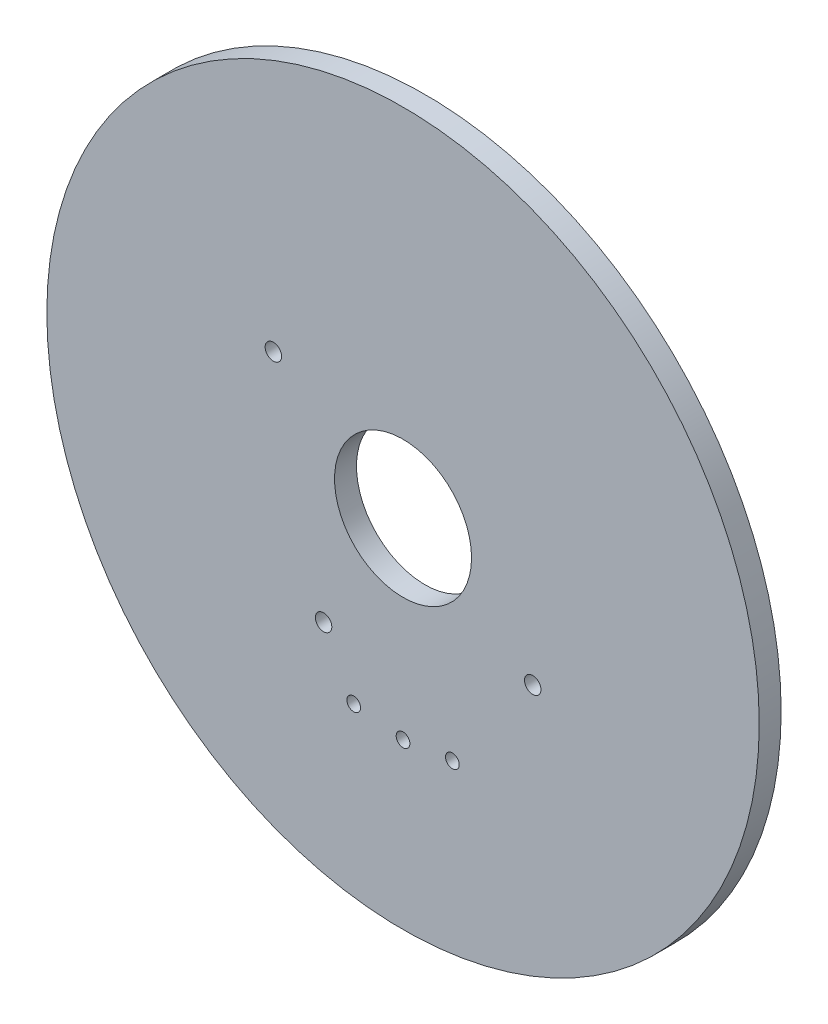
SolidWorks part; units mm, degrees
material "Fibra de vidrio-S"
ref_plane "Alzado" through (0, 0, 0) normal (0, 0, 1) x (1, 0, 0)
ref_plane "Planta" through (0, 0, 0) normal (0, 1, 0) x (1, 0, 0)
ref_plane "Vista lateral" through (0, 0, 0) normal (1, 0, 0) x (0, 0, -1)
sketch "Croquis1" plane through (0, 0, 0) normal (0, 0, 1) x (1, 0, 0)
  circle A0 centre (0, 0) radius 13
  circle A1 centre (0, 0) radius 2.5
  dimension "D1" = 5
  dimension "D2" = 26
extrude "Saliente-Extruir1" add sketch "Croquis1" along normal blind 0.8
sketch "Croquis2" plane through (0, 0, 0.8) normal (0, 0, 1) x (1, 0, 0)
  line L0 (0, -7) -> (0, 0) construction
  line L1 (0, 0) -> (-1.8, -6.7646) construction
  line L2 (-1.8, -6.7646) -> (0, -7) construction
  line L3 (0, 0) -> (1.8, -6.7646) construction
  line L4 (1.8, -6.7646) -> (0, -7) construction
  circle A0 centre (0, -7) radius 0.25
  circle A1 centre (-1.8, -6.7646) radius 0.25
  circle A2 centre (1.8, -6.7646) radius 0.25
  circle A3 centre (4.733, -2.9) radius 0.3
  circle A5 centre (-2.9, -4.733) radius 0.3
  circle A6 centre (-4.733, 2.9) radius 0.3
  circle A7 centre (2.9, 4.733) radius 0.3 [skipped]
  circle A9 centre (0, 0) radius 13 construction
  point P21 (0, 0)
  dimension "D1" = 0.5
  dimension "D4" = 0.6
  dimension "D2" = 7
  dimension "D3" = 3.6
  dimension "D6" = 2.9
  dimension "D7" = 4.733
  dimension "D5" = 4
extrude "Cortar-Extruir1" cut sketch "Croquis2" against normal blind 1.6
